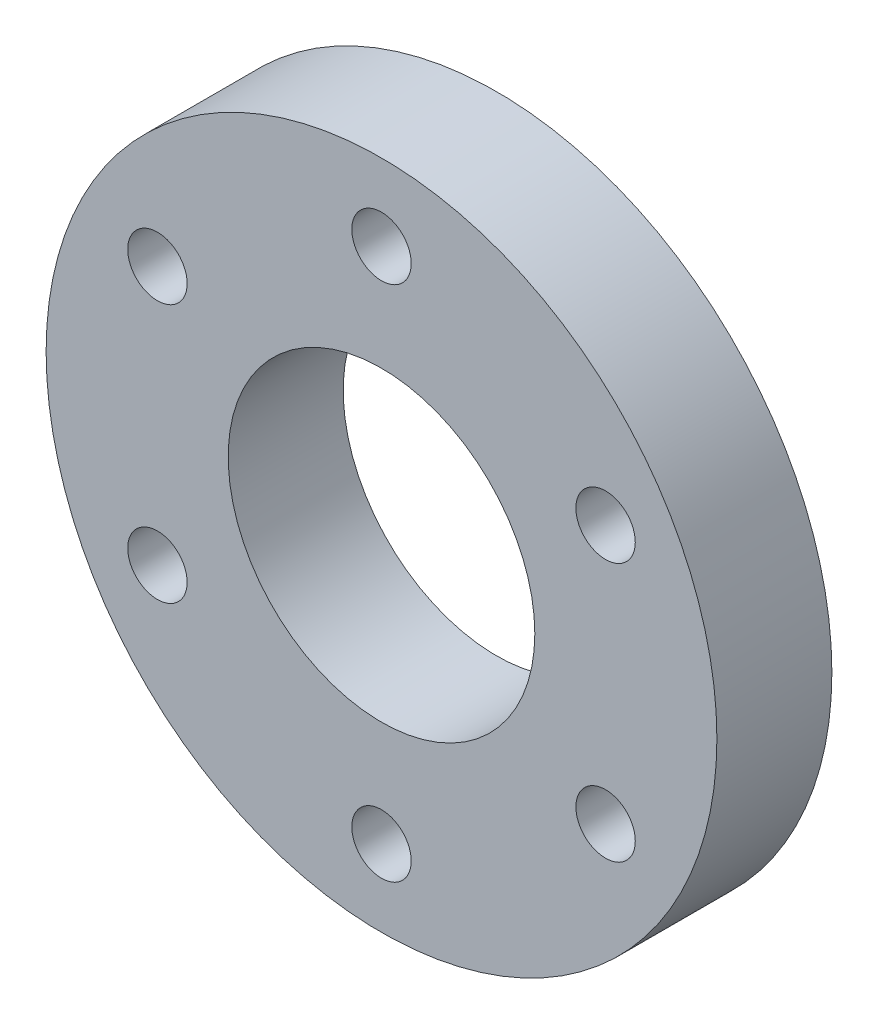
SolidWorks part; units mm, degrees
material "Thornel Mat VMA"
ref_plane "前视基准面" through (0, 0, 0) normal (0, 0, 1) x (1, 0, 0)
ref_plane "上视基准面" through (0, 0, 0) normal (0, 1, 0) x (1, 0, 0)
ref_plane "右视基准面" through (0, 0, 0) normal (1, 0, 0) x (0, 0, -1)
sketch "草图1" plane through (0, 0, 0) normal (0, 0, 1) x (1, 0, 0)
  line L0 (-11.6913, 6.75) -> (0, 0) construction
  line L1 (0, 0) -> (-11.6913, -6.75) construction
  line L2 (0, 13.5) -> (0, 0) construction
  line L3 (0, 0) -> (11.6913, 6.75) construction
  line L4 (11.6913, -6.75) -> (0, 0) construction
  line L5 (0, 0) -> (0, -13.5) construction
  circle A0 centre (0, 0) radius 17.5
  circle A1 centre (0, 0) radius 8
  circle A2 centre (0, 0) radius 13.5 construction
  circle A3 centre (0, 13.5) radius 1.55
  circle A4 centre (11.6913, -6.75) radius 1.55
  circle A5 centre (-11.6913, 6.75) radius 1.55
  circle A6 centre (-11.6913, -6.75) radius 1.55
  circle A7 centre (11.6913, 6.75) radius 1.55
  circle A8 centre (0, -13.5) radius 1.55
  dimension "D1" = 60
  dimension "D2" = 60
  dimension "D3" = 60
  dimension "D4" = 60
extrude "凸台-拉伸1" add sketch "草图1" along normal blind 6
